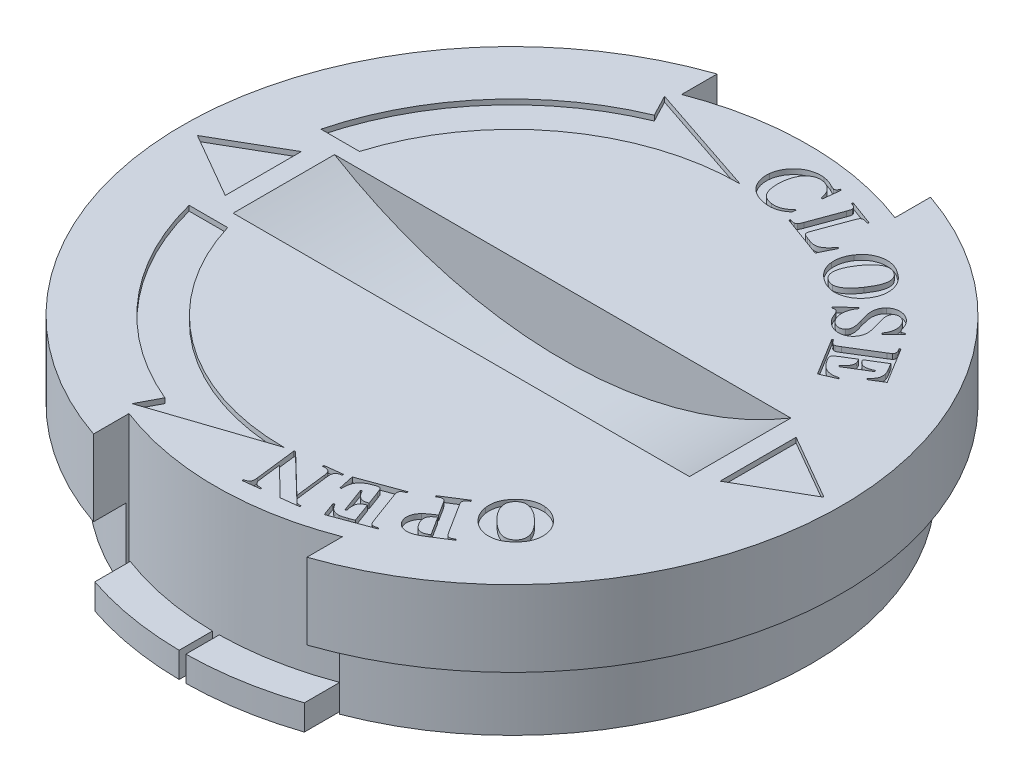
SolidWorks part; units mm, degrees
ref_plane "Front Plane" through (0, 0, 0) normal (0, 0, 1) x (1, 0, 0)
ref_plane "Top Plane" through (0, 0, 0) normal (0, 1, 0) x (1, 0, 0)
ref_plane "Right Plane" through (0, 0, 0) normal (1, 0, 0) x (0, 0, -1)
sketch "Lower Lid Body Sketch" plane through (0, 0, 0) normal (0, 1, 0) x (1, 0, 0)
  circle A0 centre (0, 0) radius 5.9
extrude "Lower Lid Body" add sketch "Lower Lid Body Sketch" along normal blind 1.5
sketch "Upper Lid Body Sketch" plane through (0, 1.5, 0) normal (0, 1, 0) x (1, 0, 0)
  circle A0 centre (0, 0) radius 6.5
extrude "Upper Lid Body" add sketch "Upper Lid Body Sketch" along normal blind 1.5
sketch "Lid Lock Cut Sketch" plane through (0, 3, 0) normal (0, 1, 0) x (1, 0, 0)
  line L0 (-2.1046, 6.1499) -> (2.1046, 6.1499) construction
  line L1 (-2.1046, 6.1499) -> (-2.1046, 5.4499)
  line L2 (2.1046, 6.1499) -> (2.1046, 5.4499)
  circle A0 centre (0, 0) radius 6.5 construction
  arc A1 (-2.1046, 5.4499) -> (2.1046, 5.4499) centre (0, 0) cw
  arc A2 (2.1046, 6.1499) -> (-2.1046, 6.1499) centre (0, 0) ccw
  point P5 (0, 6.1499)
  dimension "D1" = 0.7
extrude "Lid Lock Cut" cut sketch "Lid Lock Cut Sketch" against normal through all
sketch "Lid Lock Notch Sketch" plane through (0, 0, 0) normal (0, 1, 0) x (1, 0, 0)
  line L0 (-2.0666, 5.4644) -> (-2.0666, 6.1627)
  line L1 (2.0666, 5.4644) -> (2.0666, 6.1627)
  arc A0 (2.1046, 5.4499) -> (-2.1046, 5.4499) centre (0, 0) ccw construction
  arc A1 (2.0666, 5.4644) -> (-2.0666, 5.4644) centre (0, 0) ccw
  arc A2 (2.0666, 6.1627) -> (-2.0666, 6.1627) centre (0, 0) ccw
extrude "Lid Lock Notch" add sketch "Lid Lock Notch Sketch" along normal blind 0.5
sketch "Lid Lock Notch Split Sketch" plane through (0, 0.5, 0) normal (0, 1, 0) x (1, 0, 0)
  line L0 (0.0666, 6.4997) -> (0.0666, 5.8417)
  line L1 (-0.0666, 6.4997) -> (-0.0666, 5.8417)
  line L2 (2.0666, 5.4644) -> (2.0666, 6.1627)
  line L3 (-2.0666, 6.1627) -> (-2.0666, 5.4644)
  arc A2 (2.0666, 5.4644) -> (-2.0666, 5.4644) centre (0, 0) ccw
  arc A3 (2.0666, 6.1627) -> (-2.0666, 6.1627) centre (0, 0) ccw
  arc A4 (0.0666, 5.8417) -> (-0.0666, 5.8417) centre (0, 0) ccw
  arc A5 (0.0666, 6.4997) -> (-0.0666, 6.4997) centre (0, 0) ccw
  dimension "D2" = 2
  dimension "D3" = 2
  dimension "D1" = 0
extrude "Lid Lock Notch Split" cut sketch "Lid Lock Notch Split Sketch" against normal through all
mirror "Lid Lock Mirror" about plane through (0, 0, 0) normal (0, 0, 1) of "Lid Lock Cut", "Lid Lock Notch", "Lid Lock Notch Split"
sketch "Twist Grip Slot Sketch" plane through (0, 0, 0) normal (0, 0, 1) x (1, 0, 0)
  line L0 (6.5, 3) -> (2.1046, 3) construction
  line L1 (0, 0) -> (0, 6.0837) construction
  line L2 (-4.5, 3) -> (4.5, 3)
  arc A0 (4.5, 3) -> (-4.5, 3) centre (0, 10.475) cw
  point P8 (0, 1.75)
  dimension "D1" = 9
  dimension "D2" = 1.25
extrude "Twist Grip Slot" cut sketch "Twist Grip Slot Sketch" against normal mid plane 2
sketch "Open/Close Text Sketch" plane through (0, 3, 0) normal (0, 1, 0) x (1, 0, 0)
  line L0 (0, 4.5) -> (0, -4.5) construction
  line L1 (-4.3875, 1) -> (4.3875, 1) construction
  line L2 (4.5, 1) -> (-4.5, 1) construction
  line L3 (-4.3875, -1) -> (4.3875, -1) construction
  arc A0 (4.3875, 1) -> (0, 4.5) centre (0, 0) ccw construction
  arc A1 (0, -4.5) -> (4.3875, -1) centre (0, 0) ccw construction
  text T0 "CLOSE" font "Times New Roman" height 1
  text T1 "OPEN" font "Times New Roman" height 1
  point P8 (0, 1)
  point P11 (0, -1)
extrude "Open/Close Text Indent" cut sketch "Open/Close Text Sketch" against normal blind 0.1
sketch "Curved Arrow Sketch" plane through (0, 3, 0) normal (0, 1, 0) x (1, 0, 0)
  line L0 (0, 1) -> (-5.5, 1) construction
  line L1 (4.5, 1) -> (-4.5, 1) construction
  line L2 (0, 1) -> (0, 5.5352) construction
  line L3 (-2.0204, 4.8273) -> (-2.2417, 5.25)
  line L4 (-2.2417, 5.25) -> (0, 4.5)
  line L5 (-5.069, 1.3) -> (-4.2764, 1.3)
  arc A0 (0, 4.5) -> (-4.3081, 1.3) centre (0, 0) ccw
  arc A1 (-2.0204, 4.8273) -> (-5.069, 1.3) centre (0, 0) ccw
  dimension "D1" = 0.3
extrude "Curved Arrow Indent" cut sketch "Curved Arrow Sketch" against normal blind 0.1 contours L3 A1 L5 A0 L4
mirror "Curved Arrow Mirror" about plane through (0, 0, 0) normal (0, 0, 1) of "Curved Arrow Indent"
sketch "Triangle Arrow Sketch" plane through (0, 3, 0) normal (0, 1, 0) x (1, 0, 0)
  line L0 (-4.88, 0.724) -> (-4.88, -0.776)
  line L1 (-4.88, -0.776) -> (-6.179, -0.026)
  line L2 (-6.179, -0.026) -> (-4.88, 0.724)
  line L4 (-4.5, 1) -> (-4.5, -1) construction
  point P5 (-4.88, -0.026)
  dimension "D1" = 1.5
  dimension "D2" = 0.38
extrude "Triangle Arrow Indent" cut sketch "Triangle Arrow Sketch" against normal blind 0.1
mirror "Triangle Arrow Mirror" about plane through (0, 0, 0) normal (1, 0, 0) of "Triangle Arrow Indent"
